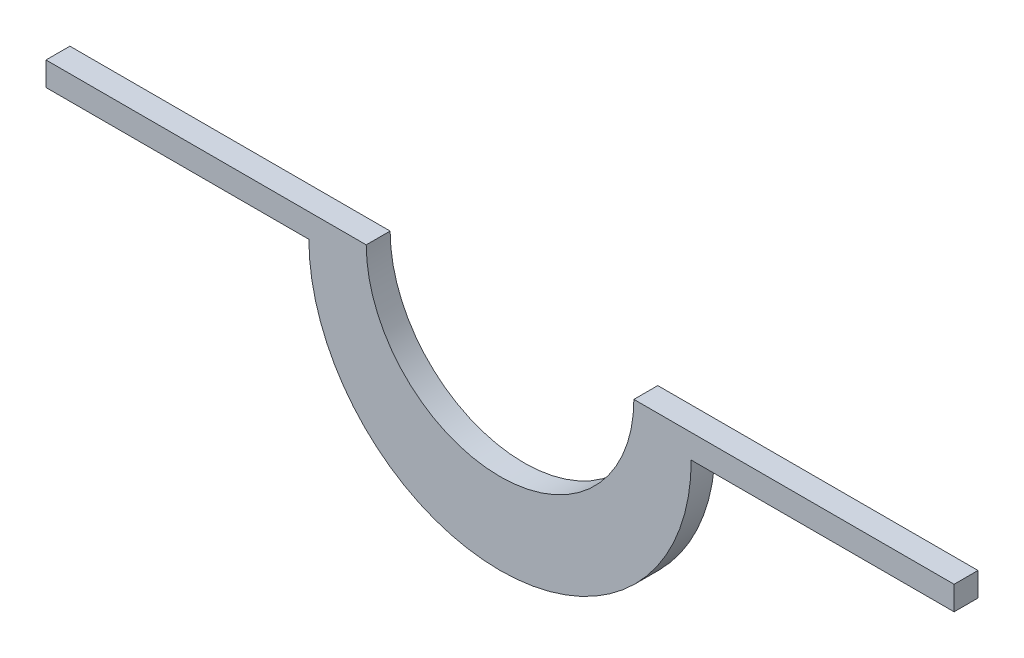
SolidWorks part; units mm, degrees
ref_plane "Plan de face" through (0, 0, 0) normal (0, 0, 1) x (1, 0, 0)
ref_plane "Plan de dessus" through (0, 0, 0) normal (0, 1, 0) x (1, 0, 0)
ref_plane "Plan de droite" through (0, 0, 0) normal (1, 0, 0) x (0, 0, -1)
sketch "Esquisse1" plane through (0, 0, 0) normal (0, 0, 1) x (1, 0, 0)
  line L0 (0, 0) -> (134, 0)
  line L1 (246, 0) -> (380, 0)
  line L2 (380, 0) -> (380, -10)
  line L3 (380, -10) -> (270, -10)
  line L4 (110, -10) -> (0, -10)
  line L5 (0, -10) -> (0, 0)
  arc A0 (134, 0) -> (246, 0) centre (190, 0) ccw
  arc A1 (270, -10) -> (110, -10) centre (190, -10) cw
  point P10 (190, -56)
  point P12 (296.3691, -10)
  dimension "D2" = 80
  dimension "D3" = 10
  dimension "D5" = 380
  dimension "D1" = 46
  dimension "D4" = 10
extrude "Boss.-Extru.1" add sketch "Esquisse1" along normal blind 10 contours L4 L5 L0 A0 L1 L2 L3 A1
